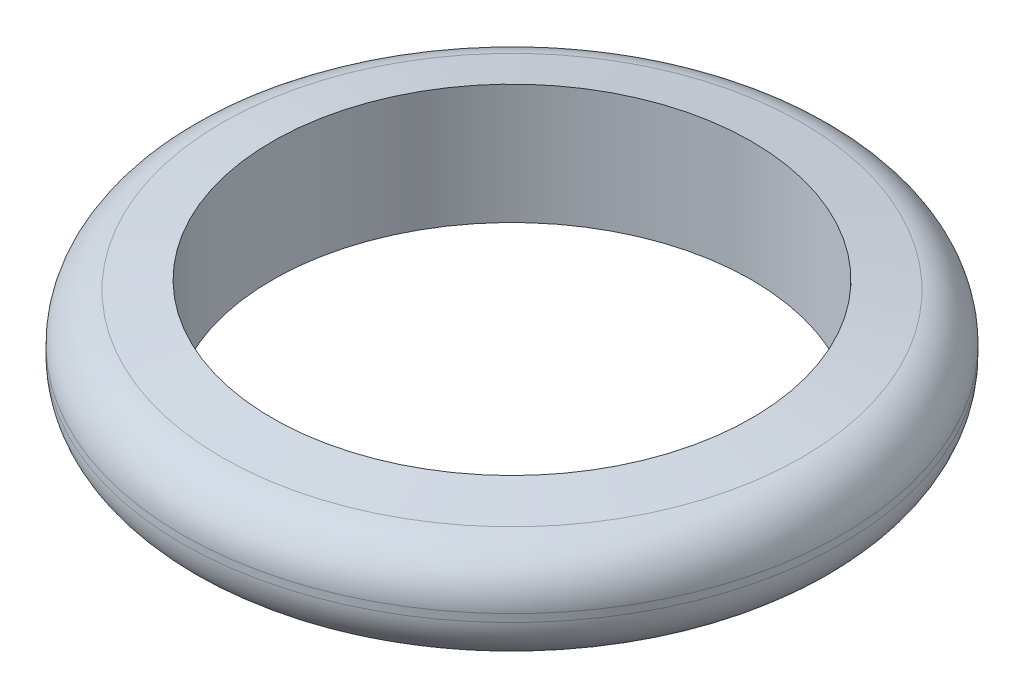
SolidWorks part; units mm, degrees
ref_plane "Front Plane" through (0, 0, 0) normal (0, 0, 1) x (1, 0, 0)
ref_plane "Top Plane" through (0, 0, 0) normal (0, 1, 0) x (1, 0, 0)
ref_plane "Right Plane" through (0, 0, 0) normal (1, 0, 0) x (0, 0, -1)
sketch "Sketch2" plane through (0, 0, 0) normal (0, 0, 1) x (1, 0, 0)
  line L0 (0, 0) -> (54.0362, 0) construction
  line L1 (0, 0) -> (0, 42.0281) construction
  line L2 (40, -10) -> (40, 10)
  line L3 (55, -7.3551) -> (55, 7.3551)
  line L4 (55, 7.3551) -> (40, 10)
  line L5 (55, -7.3551) -> (40, -10)
  dimension "D1" = 110
  dimension "D2" = 80
  dimension "D3" = 20
  dimension "D4" = 10
revolve "Revolve1" add sketch "Sketch2" angle 360 about L1
fillet "Fillet1" radius 8 2 edges at (0, -7.3551, -55) (0, 7.3551, -55)
